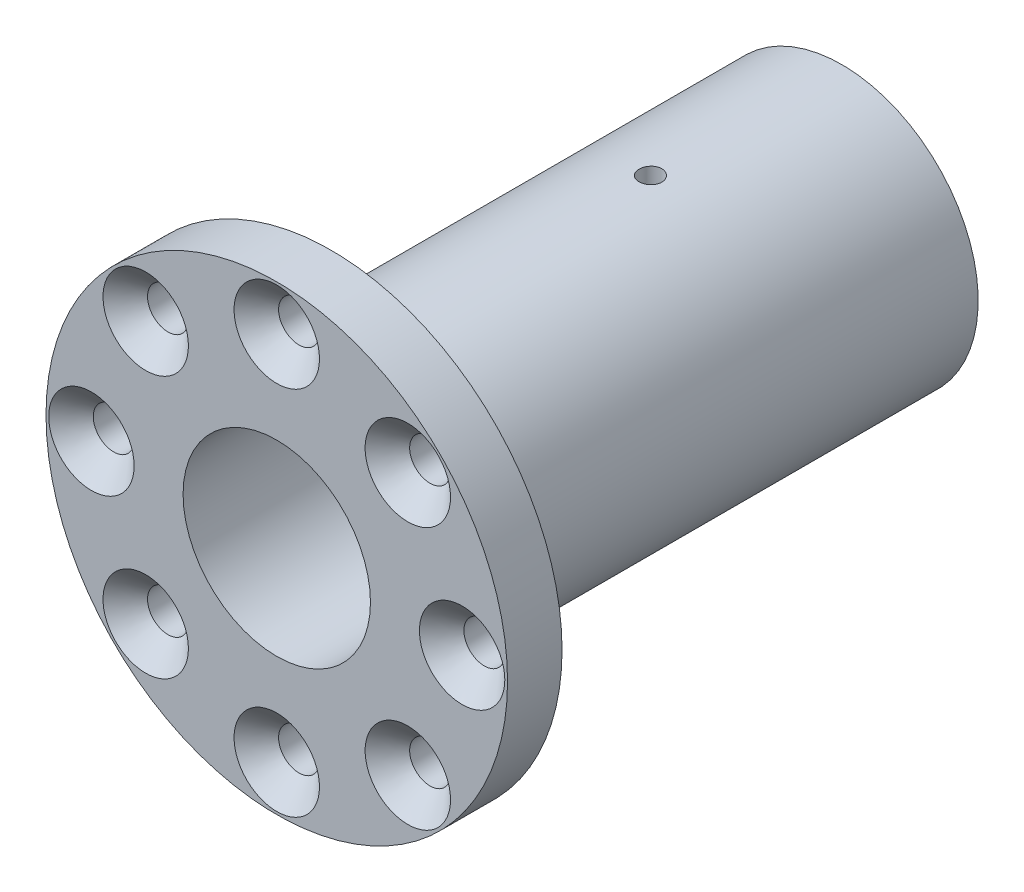
SolidWorks part; units mm, degrees
ref_plane "Front Plane" through (0, 0, 0) normal (0, 0, 1) x (1, 0, 0)
ref_plane "Top Plane" through (0, 0, 0) normal (0, 1, 0) x (1, 0, 0)
ref_plane "Right Plane" through (0, 0, 0) normal (1, 0, 0) x (0, 0, -1)
ref_plane "Plane1" through (0, 0, 0) normal (0, -1, 0) x (1, 0, 0)
sketch "Sketch1" plane through (0, 0, 0) normal (0, -1, 0) x (1, 0, 0)
  line L0 (25.4, 61.54) -> (0, 61.54)
  line L1 (0, 61.54) -> (0, 55.54)
  line L2 (0, 55.54) -> (25.4, 55.54)
  line L3 (25.4, 55.54) -> (25.4, 61.54)
  line L4 (0, 61.54) -> (0, 55.54) construction
revolve "Revolve1" add sketch "Sketch1" angle 360 about L4
sketch "Sketch2" plane through (0, 0, 55.54) normal (0, 0, -1) x (-1, 0, 0)
  circle A0 centre (0, 0) radius 15
extrude "Boss-Extrude1" add sketch "Sketch2" along normal blind 56.2
sketch "Sketch3" plane through (0, 0, -0.66) normal (0, 0, -1) x (-1, 0, 0)
  line L0 (2.5, 9.0585) -> (-2.5, 9.0585)
  line L1 (-2.5, 9.0585) -> (-2.5, 6.5383)
  line L2 (2.5, 6.5383) -> (2.5, 9.0585)
  arc A0 (-2.5, 6.5383) -> (2.5, 6.5383) centre (0, 0) cw
extrude "Cut-Extrude1" cut sketch "Sketch3" against normal through all
sketch "Sketch4" plane through (0, 0, 0) normal (0, -1, 0) x (1, 0, 0)
  line L0 (7.0104, 61.54) -> (0, 61.54)
  line L1 (0, 61.54) -> (0, -3.8786)
  line L2 (0, -3.8786) -> (7.0104, -3.8786)
  line L3 (7.0104, -3.8786) -> (7.0104, 61.54)
  line L4 (0, 61.54) -> (0, -3.8786) construction
  dimension "D1" = 7.0104
revolve "Cut-Revolve1" cut sketch "Sketch4" angle 360 about L4
hole_wizard "#2 Clearance Hole1" positions "Sketch6" profile "Sketch5" hole size "#2" standard "ANSI Inch"
sketch "Sketch6" plane through (0, 0, -0.66) normal (0, 0, -1) x (-1, 0, 0)
  point P0 (-11.5, 0)
  point P1 (-5.75, -9.9593)
  point P2 (5.75, -9.9593)
  point P3 (11.5, 0)
  point P4 (5.75, 9.9593)
  point P5 (-5.75, 9.9593)
sketch "Sketch5" plane through (11.5, 0, -0.66) normal (1, 0, 0) x (0, 1, 0)
  line L0 (0, 0) -> (0, 12)
  line L1 (0, 12) -> (1.25, 12)
  line L2 (1.25, 12) -> (1.25, 0)
  line L5 (1.25, 0) -> (0, 0)
  line L10 (0, 12) -> (-1.25, 12) construction
  line L11 (0, -6.35) -> (0, 107.95) construction
  dimension "Hole Dia." = 2.5
  dimension "Hole Depth" = 12
  dimension "Drill Angle" = 180
hole_wizard "#2 Clearance Hole2" positions "Sketch8" profile "Sketch7" hole size "#2" standard "ANSI Inch"
sketch "Sketch8" plane through (0, 9.0585, 0) normal (0, -1, 0) x (-1, 0, 0)
  line L0 (15, 0.66) -> (-15, 0.66) construction
  point P0 (0, -20.422)
  dimension "D1" = 21.082
sketch "Sketch7" plane through (0, 9.0585, 20.422) normal (1, 0, 0) x (0, 0, -1)
  line L0 (0, 0) -> (0, 16.3415)
  line L1 (0, 16.3415) -> (1.25, 16.3415)
  line L2 (1.25, 16.3415) -> (1.25, 0)
  line L5 (1.25, 0) -> (0, 0)
  line L11 (0, -6.35) -> (0, 107.95) construction
  dimension "Thru Hole Dia." = 2.5
  dimension "Thru Hole Depth" = 16.3415
hole_wizard "CSK for #8 Flat Head Machine Screw (100)1" positions "Sketch10" profile "Sketch9" countersink size "#8" standard "ANSI Inch"
sketch "Sketch10" plane through (0, 0, 61.54) normal (0, 0, 1) x (1, 0, 0)
  point P0 (0, 20.4)
  point P1 (14.425, 14.425)
  point P2 (20.4, 0)
  point P3 (14.425, -14.425)
  point P4 (0, -20.4)
  point P5 (-14.425, -14.425)
  point P6 (-20.4, 0)
  point P7 (-14.425, 14.425)
sketch "Sketch9" plane through (0, 20.4, 61.54) normal (1, 0, 0) x (0, -1, 0)
  line L0 (0, 0) -> (0, 62.2)
  line L1 (0, 62.2) -> (2.25, 62.2)
  line L2 (2.25, 62.2) -> (2.25, 2.45)
  line L3 (2.25, 2.45) -> (4.7, 0)
  line L5 (4.7, 0) -> (0, 0)
  line L6 (-2.25, 2.45) -> (-4.7, 0) construction
  line L11 (0, -6.35) -> (0, 107.95) construction
  dimension "Thru Hole Dia." = 4.5
  dimension "Thru Hole Depth" = 62.2
  dimension "Near C'Sink Dia." = 9.4
  dimension "Near C'Sink Angle" = 90
sketch "Sketch11" plane through (0, 0, 61.54) normal (0, 0, 1) x (1, 0, 0)
  circle A0 centre (0, 0) radius 10.3124
  dimension "D1" = 20.6248
extrude "Cut-Extrude2" cut sketch "Sketch11" against normal blind 38.1
